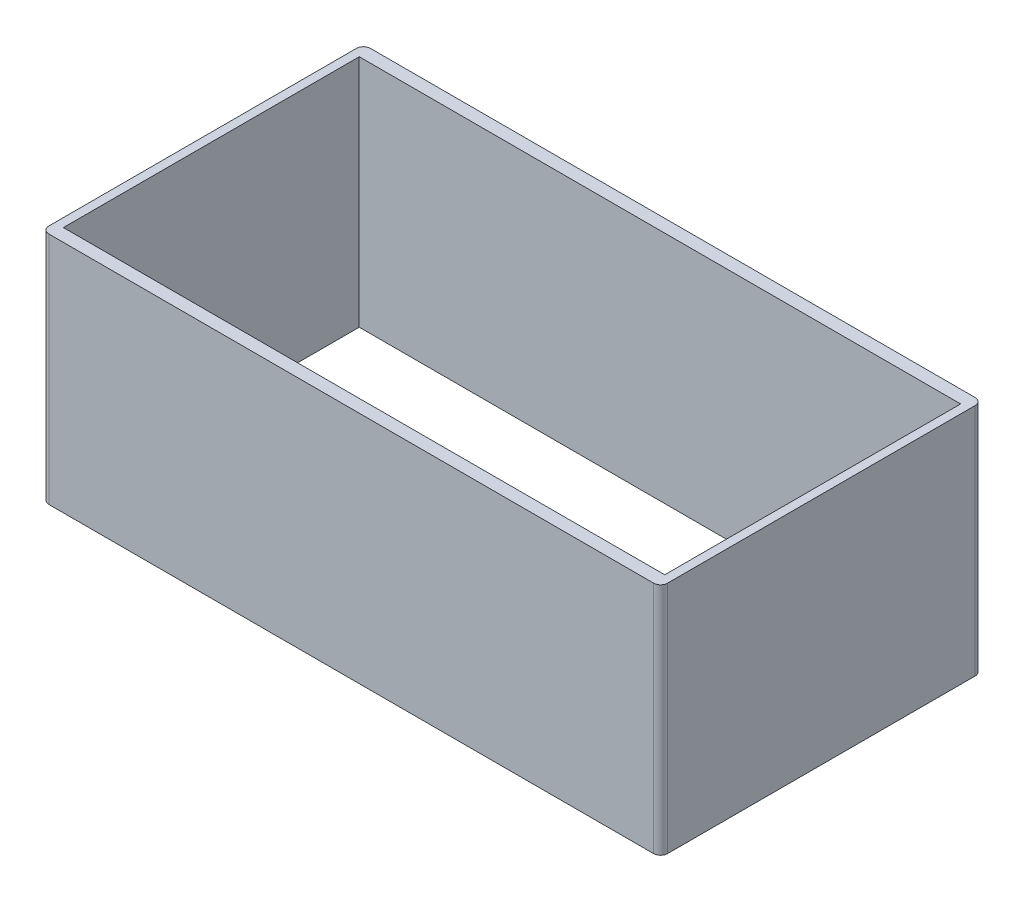
SolidWorks part; units mm, degrees
ref_plane "Alzado" through (0, 0, 0) normal (0, 0, 1) x (1, 0, 0)
ref_plane "Planta" through (0, 0, 0) normal (0, 1, 0) x (1, 0, 0)
ref_plane "Vista lateral" through (0, 0, 0) normal (1, 0, 0) x (0, 0, -1)
sketch "Middle-cover-sketch-01" plane through (0, 0, 0) normal (0, 1, 0) x (1, 0, 0)
  line L1 (-22.185, 11.53) -> (22.185, 11.53)
  line L2 (-22.185, 11.53) -> (-22.185, -11.53)
  line L3 (-22.185, -11.53) -> (22.185, -11.53)
  line L4 (22.185, 11.53) -> (22.185, -11.53)
  line L5 (-22.185, 11.53) -> (22.185, -11.53) construction
  line L6 (-22.185, -11.53) -> (22.185, 11.53) construction
  line L7 (-20.105, -9.1) -> (20.105, -9.1) construction
  line L8 (-20.105, -9.1) -> (-20.105, 9.1) construction
  line L9 (-20.105, 9.1) -> (20.105, 9.1) construction
  line L10 (20.105, -9.1) -> (20.105, 9.1) construction
  line L11 (-20.105, -9.1) -> (20.105, 9.1) construction
  line L12 (-20.105, 9.1) -> (20.105, -9.1) construction
  circle A0 centre (-20.105, 9.1) radius 0.85
  circle A1 centre (20.105, 9.1) radius 0.85
  circle A2 centre (20.105, -9.1) radius 0.85
  circle A3 centre (-20.105, -9.1) radius 0.85
  point P0 (0, 0)
  point P6 (0, 0)
  dimension "D5" = 1.7
  dimension "D1" = 23.06
  dimension "D2" = 44.37
  dimension "D3" = 18.2
  dimension "D4" = 40.21
extrude "Saliente-Extruir1" add sketch "Middle-cover-sketch-01" along normal blind 16.8 contours L3 L4 L1 L2
shell "Vaciado1" thickness 1
fillet "Redondeo1" radius 0.5 4 edges at (-22.185, 8.4, -11.53) (22.185, 8.4, -11.53) (-22.185, 8.4, 11.53) (22.185, 8.4, 11.53)
